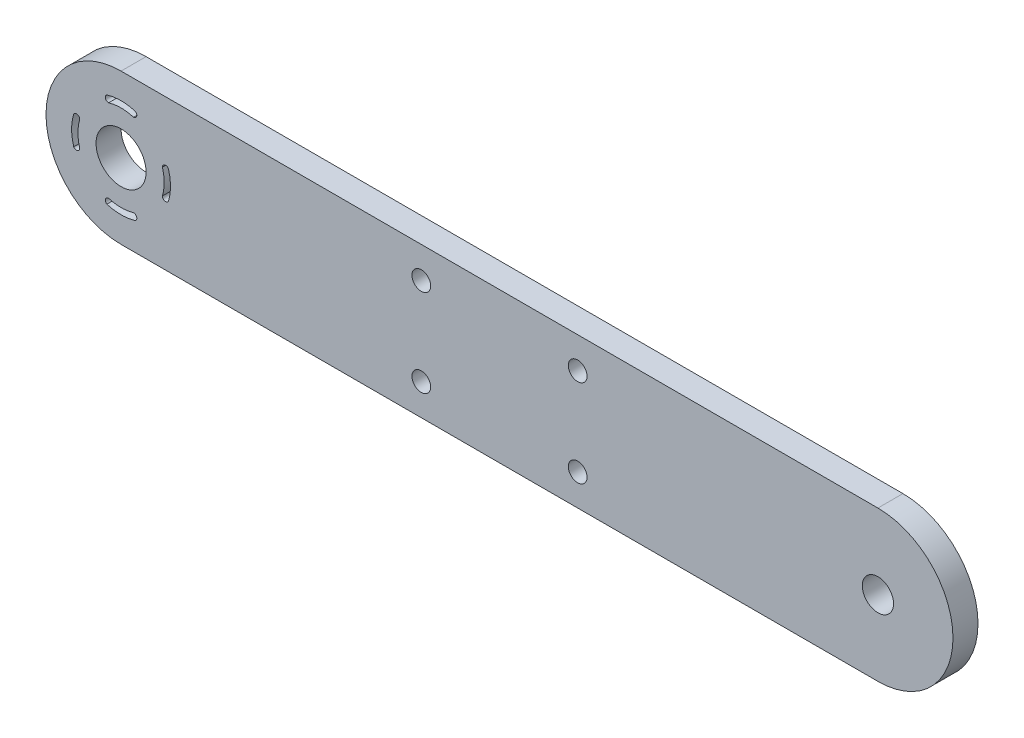
SolidWorks part; units mm, degrees
material "Beech"
ref_plane "Front Plane" through (0, 0, 0) normal (0, 0, 1) x (1, 0, 0)
ref_plane "Top Plane" through (0, 0, 0) normal (0, 1, 0) x (1, 0, 0)
ref_plane "Right Plane" through (0, 0, 0) normal (1, 0, 0) x (0, 0, -1)
sketch "Sketch1" plane through (0, 0, 0) normal (0, 0, 1) x (1, 0, 0)
  line L0 (12, 24) -> (133, 24)
  line L1 (133, 0) -> (12, 0)
  circle A0 centre (12, 12) radius 4
  arc A1 (12, 24) -> (12, 0) centre (12, 12) ccw
  arc A2 (133, 0) -> (133, 24) centre (133, 12) ccw
  circle A3 centre (60, 5) radius 1.5
  circle A4 centre (60, 19) radius 1.5
  circle A5 centre (85, 5) radius 1.5
  circle A6 centre (85, 19) radius 1.5
  circle A7 centre (133, 12) radius 2.5
  arc A8 (9.7297, 4.4333) -> (14.2703, 4.4333) centre (12, 12) ccw
  arc A9 (19.5667, 9.7297) -> (19.5667, 14.2703) centre (12, 12) ccw
  arc A10 (14.2703, 19.5667) -> (9.7297, 19.5667) centre (12, 12) ccw
  arc A11 (4.4333, 14.2703) -> (4.4333, 9.7297) centre (12, 12) ccw
  arc A12 (10, 5.3961) -> (14, 5.3961) centre (12, 12) ccw
  arc A13 (18.6039, 10) -> (18.6039, 14) centre (12, 12) ccw
  arc A14 (14, 18.6039) -> (10, 18.6039) centre (12, 12) ccw
  arc A15 (5.3961, 14) -> (5.3961, 10) centre (12, 12) ccw
  arc A16 (14.2703, 4.4333) -> (14, 5.3961) centre (14, 4.8768) ccw
  arc A17 (10, 5.3961) -> (9.7297, 4.4333) centre (10, 4.8768) ccw
  arc A18 (4.4333, 9.7297) -> (5.3961, 10) centre (4.8768, 10) ccw
  arc A19 (5.3961, 14) -> (4.4333, 14.2703) centre (4.8768, 14) ccw
  arc A20 (19.5667, 14.2703) -> (18.6039, 14) centre (19.1232, 14) ccw
  arc A21 (18.6039, 10) -> (19.5667, 9.7297) centre (19.1232, 10) ccw
  arc A22 (9.7297, 19.5667) -> (10, 18.6039) centre (10, 19.1232) ccw
  arc A23 (14, 18.6039) -> (14.2703, 19.5667) centre (14, 19.1232) ccw
extrude "Boss-Extrude1" add sketch "Sketch1" along normal blind 4
